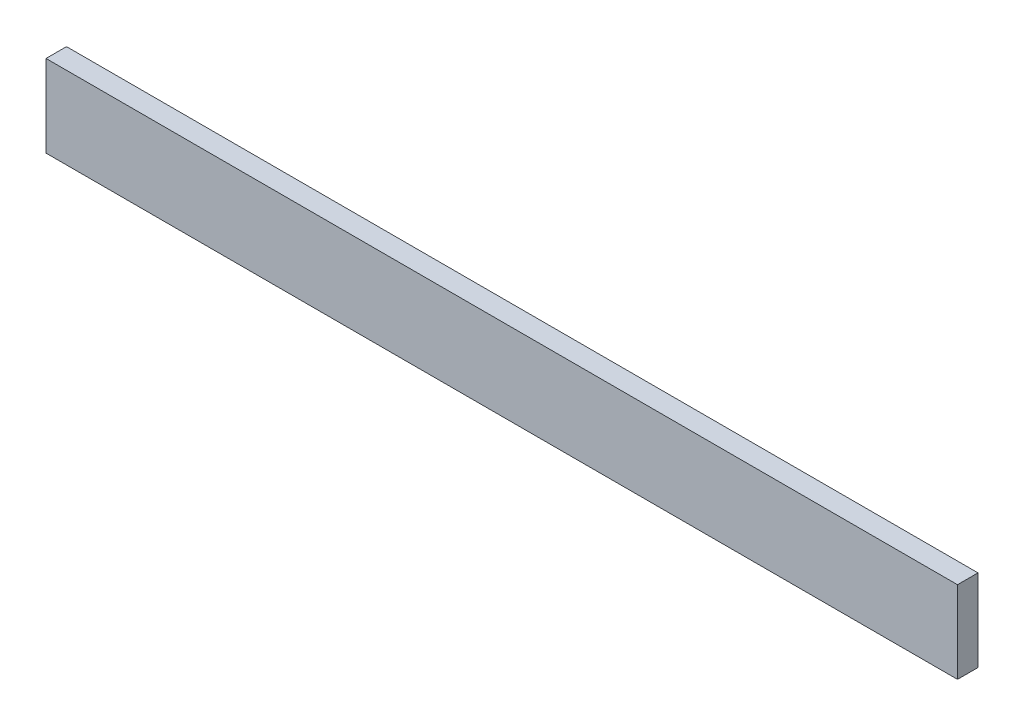
SolidWorks part; units mm, degrees
material "Silicon Rubber"
ref_plane "Front" through (0, 0, 0) normal (0, 0, 1) x (1, 0, 0)
ref_plane "Top" through (0, 0, 0) normal (0, 1, 0) x (1, 0, 0)
ref_plane "Right" through (0, 0, 0) normal (1, 0, 0) x (0, 0, -1)
sketch "Sketch1" plane through (0, 0, 0) normal (0, 0, 1) x (1, 0, 0)
  line L1 (-25.5301, -77.4786) -> (115.6403, -77.4786)
  line L2 (-25.5301, -77.4786) -> (-25.5301, -64.7786)
  line L3 (-25.5301, -64.7786) -> (115.6403, -64.7786)
  line L4 (115.6403, -77.4786) -> (115.6403, -64.7786)
  line L5 (115.6403, -77.4786) -> (-25.3505, -77.4786) construction
  line L7 (115.6403, -77.4786) -> (115.6403, -63.6102) construction
  line L8 (-25.5301, -77.4786) -> (-25.5301, -67.5218) construction
  point P0 (0, 0)
  dimension "D1" = 12.7
extrude "Boss-Extrude1" add sketch "Sketch1" along normal blind 3.175
